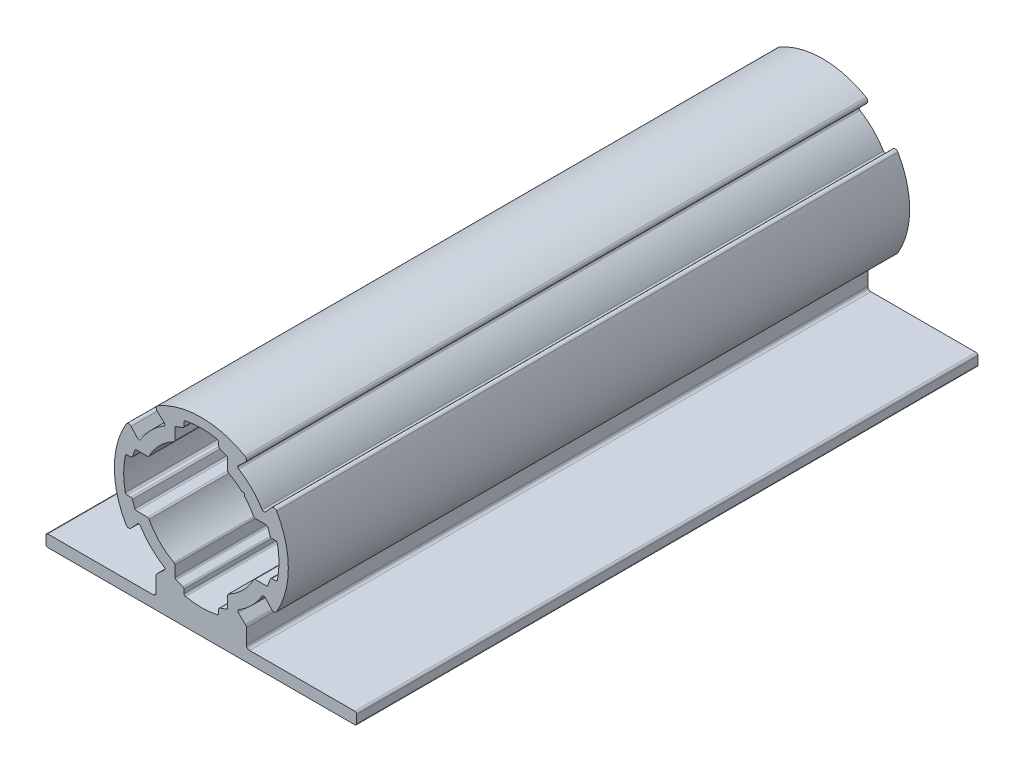
SolidWorks part; units mm, degrees
ref_plane "前视基准面" through (0, 0, 0) normal (0, 0, 1) x (1, 0, 0)
ref_plane "上视基准面" through (0, 0, 0) normal (0, 1, 0) x (1, 0, 0)
ref_plane "右视基准面" through (0, 0, 0) normal (1, 0, 0) x (0, 0, -1)
sketch "Model" plane through (0, 0, 0) normal (0, 0, 1) x (1, 0, 0)
  line L0 (1440.8676, 579.1075) -> (1452.8073, 579.1075)
  line L1 (1452.8073, 579.1075) -> (1457.8073, 579.1075)
  line L2 (1458.1073, 578.8075) -> (1458.1073, 577.5075)
  line L3 (1408.4073, 577.2075) -> (1457.8073, 577.2075)
  line L4 (1408.1073, 578.8075) -> (1408.1073, 577.5075)
  line L5 (1408.4073, 579.1075) -> (1425.347, 579.1075)
  line L6 (1425.847, 582.0221) -> (1425.847, 579.6075)
  line L7 (1426.0079, 582.3895) -> (1427.1364, 583.4313)
  line L8 (1421.7893, 586.608) -> (1422.8311, 587.7366)
  line L9 (1421.7893, 600.8069) -> (1422.8311, 599.6783)
  line L10 (1426.0079, 605.0255) -> (1427.1364, 603.9836)
  line L11 (1440.2067, 605.0255) -> (1439.0781, 603.9836)
  line L12 (1444.4253, 600.8069) -> (1443.3834, 599.6783)
  line L13 (1444.4253, 586.608) -> (1443.3834, 587.7366)
  line L14 (1440.2067, 582.3895) -> (1439.0781, 583.4313)
  line L15 (1440.3676, 582.0221) -> (1440.3676, 579.6075)
  line L16 (1421.1662, 590.9075) -> (1421.7541, 590.9075)
  line L17 (1422.017, 590.7238) -> (1422.412, 589.6461)
  line L18 (1422.6749, 589.4624) -> (1424.425, 589.4624)
  line L19 (1428.8622, 585.0252) -> (1428.8622, 583.2751)
  line L20 (1429.0459, 583.0122) -> (1430.1237, 582.6171)
  line L21 (1430.3073, 582.3543) -> (1430.3073, 581.7664)
  line L22 (1435.9073, 581.7664) -> (1435.9073, 582.3543)
  line L23 (1436.0909, 582.6171) -> (1437.1687, 583.0122)
  line L24 (1437.3524, 583.2751) -> (1437.3524, 585.0252)
  line L25 (1441.7896, 589.4624) -> (1443.5397, 589.4624)
  line L26 (1443.8026, 589.6461) -> (1444.1976, 590.7238)
  line L27 (1444.4605, 590.9075) -> (1445.0484, 590.9075)
  line L28 (1445.0484, 596.5075) -> (1444.4605, 596.5075)
  line L29 (1444.1976, 596.6911) -> (1443.8026, 597.7689)
  line L30 (1443.5397, 597.9525) -> (1441.7896, 597.9525)
  line L31 (1437.3524, 602.3898) -> (1437.3524, 604.1399)
  line L32 (1437.1687, 604.4028) -> (1436.0909, 604.7978)
  line L33 (1435.9073, 605.0607) -> (1435.9073, 605.6486)
  line L34 (1430.3073, 605.6486) -> (1430.3073, 605.0607)
  line L35 (1430.1237, 604.7978) -> (1429.0459, 604.4028)
  line L36 (1428.8622, 604.1399) -> (1428.8622, 602.3898)
  line L37 (1424.425, 597.9525) -> (1422.6749, 597.9525)
  line L38 (1422.412, 597.7689) -> (1422.017, 596.6911)
  line L39 (1421.7541, 596.5075) -> (1421.1662, 596.5075)
  line L40 (1440.0369, 600.6371) -> (1440.0369, 600.2059)
  line L41 (1440.0369, 600.6371) -> (1439.6058, 600.6371)
  arc A0 (1421.1662, 596.5075) -> (1420.8726, 596.269) centre (1421.1662, 596.2075) ccw
  arc A1 (1458.1073, 578.8075) -> (1457.8073, 579.1075) centre (1457.8073, 578.8075) ccw
  arc A2 (1457.8073, 577.2075) -> (1458.1073, 577.5075) centre (1457.8073, 577.5075) ccw
  arc A3 (1408.1073, 577.5075) -> (1408.4073, 577.2075) centre (1408.4073, 577.5075) ccw
  arc A4 (1408.4073, 579.1075) -> (1408.1073, 578.8075) centre (1408.4073, 578.8075) ccw
  arc A5 (1425.347, 579.1075) -> (1425.847, 579.6075) centre (1425.347, 579.6075) ccw
  arc A6 (1426.0079, 582.3895) -> (1425.847, 582.0221) centre (1426.347, 582.0221) ccw
  arc A7 (1427.1364, 583.4313) -> (1427.0899, 583.9074) centre (1426.9329, 583.6518) ccw
  arc A8 (1423.3072, 587.6901) -> (1427.0899, 583.9074) centre (1433.1073, 593.7075) ccw
  arc A9 (1423.3072, 587.6901) -> (1422.8311, 587.7366) centre (1423.0516, 587.5331) ccw
  arc A10 (1420.9891, 586.6968) -> (1421.7893, 586.608) centre (1421.4219, 586.9472) ccw
  arc A11 (1420.9891, 600.7181) -> (1420.9891, 586.6968) centre (1433.1073, 593.7075) ccw
  arc A12 (1421.7893, 600.8069) -> (1420.9891, 600.7181) centre (1421.4219, 600.4678) ccw
  arc A13 (1422.8311, 599.6783) -> (1423.3072, 599.7249) centre (1423.0516, 599.8818) ccw
  arc A14 (1427.0899, 603.5075) -> (1423.3072, 599.7249) centre (1433.1073, 593.7075) ccw
  arc A15 (1427.0899, 603.5075) -> (1427.1364, 603.9836) centre (1426.9329, 603.7632) ccw
  arc A16 (1426.0966, 605.8257) -> (1426.0079, 605.0255) centre (1426.347, 605.3929) ccw
  arc A17 (1440.118, 605.8257) -> (1426.0966, 605.8257) centre (1433.1073, 593.7075) ccw
  arc A18 (1440.2067, 605.0255) -> (1440.118, 605.8257) centre (1439.8676, 605.3929) ccw
  arc A19 (1439.0781, 603.9836) -> (1439.1247, 603.5075) centre (1439.2816, 603.7632) ccw
  arc A20 (1442.9074, 599.7249) -> (1439.1247, 603.5075) centre (1433.1073, 593.7075) ccw
  arc A21 (1442.9074, 599.7249) -> (1443.3834, 599.6783) centre (1443.163, 599.8818) ccw
  arc A22 (1445.2255, 600.7181) -> (1444.4253, 600.8069) centre (1444.7927, 600.4678) ccw
  arc A23 (1445.2255, 586.6968) -> (1445.2255, 600.7181) centre (1433.1073, 593.7075) ccw
  arc A24 (1444.4253, 586.608) -> (1445.2255, 586.6968) centre (1444.7927, 586.9472) ccw
  arc A25 (1443.3834, 587.7366) -> (1442.9074, 587.6901) centre (1443.163, 587.5331) ccw
  arc A26 (1439.1247, 583.9074) -> (1442.9074, 587.6901) centre (1433.1073, 593.7075) ccw
  arc A27 (1439.1247, 583.9074) -> (1439.0781, 583.4313) centre (1439.2816, 583.6518) ccw
  arc A28 (1440.3676, 582.0221) -> (1440.2067, 582.3895) centre (1439.8676, 582.0221) ccw
  arc A29 (1440.3676, 579.6075) -> (1440.8676, 579.1075) centre (1440.8676, 579.6075) ccw
  arc A30 (1420.8726, 596.269) -> (1420.8726, 591.146) centre (1433.1073, 593.7075) ccw
  arc A31 (1420.8726, 591.146) -> (1421.1662, 590.9075) centre (1421.1662, 591.2075) ccw
  arc A32 (1422.017, 590.7238) -> (1421.7541, 590.9075) centre (1421.7541, 590.6275) ccw
  arc A33 (1422.412, 589.6461) -> (1422.6749, 589.4624) centre (1422.6749, 589.7424) ccw
  arc A34 (1424.6908, 589.3015) -> (1424.425, 589.4624) centre (1424.425, 589.1624) ccw
  arc A35 (1424.6908, 589.3015) -> (1428.7014, 585.291) centre (1433.1073, 593.7075) ccw
  arc A36 (1428.8622, 585.0252) -> (1428.7014, 585.291) centre (1428.5622, 585.0252) ccw
  arc A37 (1428.8622, 583.2751) -> (1429.0459, 583.0122) centre (1429.1422, 583.2751) ccw
  arc A38 (1430.3073, 582.3543) -> (1430.1237, 582.6171) centre (1430.0273, 582.3543) ccw
  arc A39 (1430.3073, 581.7664) -> (1430.5458, 581.4727) centre (1430.6073, 581.7664) ccw
  arc A40 (1430.5458, 581.4727) -> (1435.6688, 581.4727) centre (1433.1073, 593.7075) ccw
  arc A41 (1435.6688, 581.4727) -> (1435.9073, 581.7664) centre (1435.6073, 581.7664) ccw
  arc A42 (1436.0909, 582.6171) -> (1435.9073, 582.3543) centre (1436.1873, 582.3543) ccw
  arc A43 (1437.1687, 583.0122) -> (1437.3524, 583.2751) centre (1437.0724, 583.2751) ccw
  arc A44 (1437.5132, 585.291) -> (1437.3524, 585.0252) centre (1437.6524, 585.0252) ccw
  arc A45 (1437.5132, 585.291) -> (1441.5238, 589.3015) centre (1433.1073, 593.7075) ccw
  arc A46 (1441.7896, 589.4624) -> (1441.5238, 589.3015) centre (1441.7896, 589.1624) ccw
  arc A47 (1443.5397, 589.4624) -> (1443.8026, 589.6461) centre (1443.5397, 589.7424) ccw
  arc A48 (1444.4605, 590.9075) -> (1444.1976, 590.7238) centre (1444.4605, 590.6275) ccw
  arc A49 (1445.0484, 590.9075) -> (1445.342, 591.146) centre (1445.0484, 591.2075) ccw
  arc A50 (1445.342, 591.146) -> (1445.342, 596.269) centre (1433.1073, 593.7075) ccw
  arc A51 (1445.342, 596.269) -> (1445.0484, 596.5075) centre (1445.0484, 596.2075) ccw
  arc A52 (1444.1976, 596.6911) -> (1444.4605, 596.5075) centre (1444.4605, 596.7875) ccw
  arc A53 (1443.8026, 597.7689) -> (1443.5397, 597.9525) centre (1443.5397, 597.6725) ccw
  arc A54 (1441.5238, 598.1134) -> (1441.7896, 597.9525) centre (1441.7896, 598.2525) ccw
  arc A55 (1441.5238, 598.1134) -> (1440.0369, 600.2059) centre (1433.1073, 593.7075) ccw
  arc A56 (1439.6058, 600.6371) -> (1437.5132, 602.124) centre (1433.1073, 593.7075) ccw
  arc A57 (1437.3524, 602.3898) -> (1437.5132, 602.124) centre (1437.6524, 602.3898) ccw
  arc A58 (1437.3524, 604.1399) -> (1437.1687, 604.4028) centre (1437.0724, 604.1399) ccw
  arc A59 (1435.9073, 605.0607) -> (1436.0909, 604.7978) centre (1436.1873, 605.0607) ccw
  arc A60 (1435.9073, 605.6486) -> (1435.6688, 605.9422) centre (1435.6073, 605.6486) ccw
  arc A61 (1435.6688, 605.9422) -> (1430.5458, 605.9422) centre (1433.1073, 593.7075) ccw
  arc A62 (1430.5458, 605.9422) -> (1430.3073, 605.6486) centre (1430.6073, 605.6486) ccw
  arc A63 (1430.1237, 604.7978) -> (1430.3073, 605.0607) centre (1430.0273, 605.0607) ccw
  arc A64 (1429.0459, 604.4028) -> (1428.8622, 604.1399) centre (1429.1422, 604.1399) ccw
  arc A65 (1428.7014, 602.124) -> (1428.8622, 602.3898) centre (1428.5622, 602.3898) ccw
  arc A66 (1428.7014, 602.124) -> (1424.6908, 598.1134) centre (1433.1073, 593.7075) ccw
  arc A67 (1424.425, 597.9525) -> (1424.6908, 598.1134) centre (1424.425, 598.2525) ccw
  arc A68 (1422.6749, 597.9525) -> (1422.412, 597.7689) centre (1422.6749, 597.6725) ccw
  arc A69 (1421.7541, 596.5075) -> (1422.017, 596.6911) centre (1421.7541, 596.7875) ccw
extrude "凸台-拉伸1" add sketch "Model" along normal blind 100
